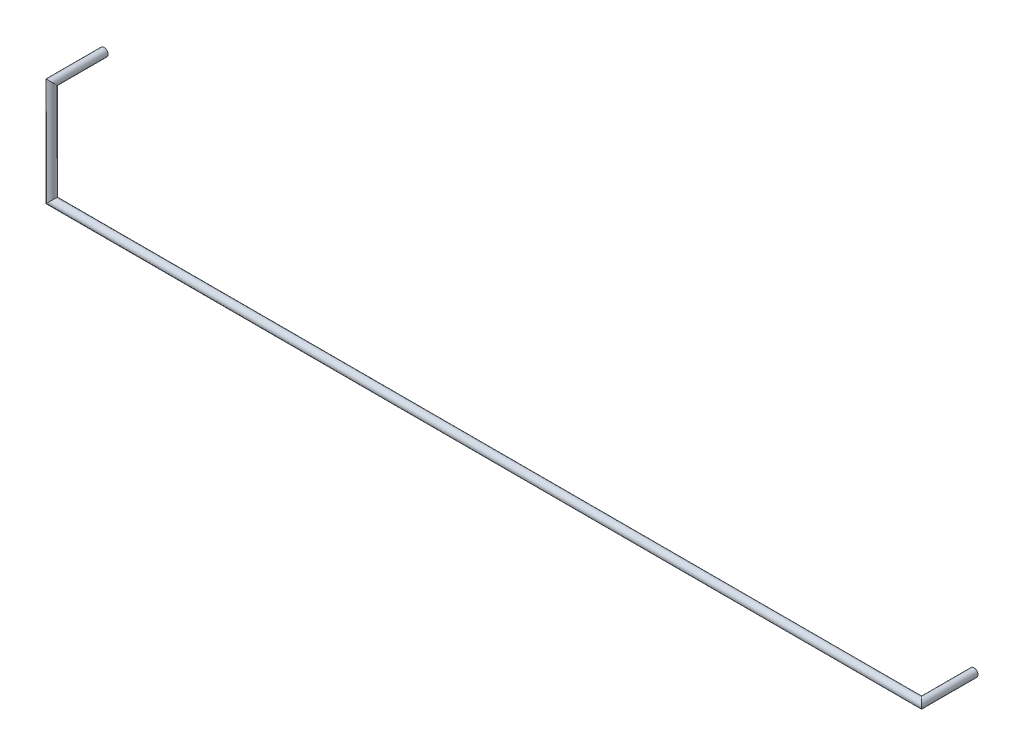
SolidWorks part; units mm, degrees
ref_plane "Front Plane" through (0, 0, 0) normal (0, 0, 1) x (1, 0, 0)
ref_plane "Top Plane" through (0, 0, 0) normal (0, 1, 0) x (1, 0, 0)
ref_plane "Right Plane" through (0, 0, 0) normal (1, 0, 0) x (0, 0, -1)
sketch3d "3DSketch3"
  line L0 (0, 0, 0) -> (0, 0, 2.6)
  line L1 (0, 0, 2.6) -> (0, -5.08, 2.6)
  line L2 (0, -5.08, 2.6) -> (43.18, -5.08, 2.6)
  line L3 (43.18, -5.08, 2.6) -> (43.18, -5.08, 0)
  dimension "D2" = 2.6
  dimension "D1" = 2.6
  dimension "D4" = 43.18
  dimension "D3" = 5.08
sweep "Sweep1" add path "3DSketch3" circular profile diameter 0.4 parameters "D3"=0.4
equation "\"D2@3DSketch3\"=\"D1@3DSketch3\""
equation "\"D4@3DSketch3\"=2.54*17"
equation "\"D3@3DSketch3\"=2.54*2"
